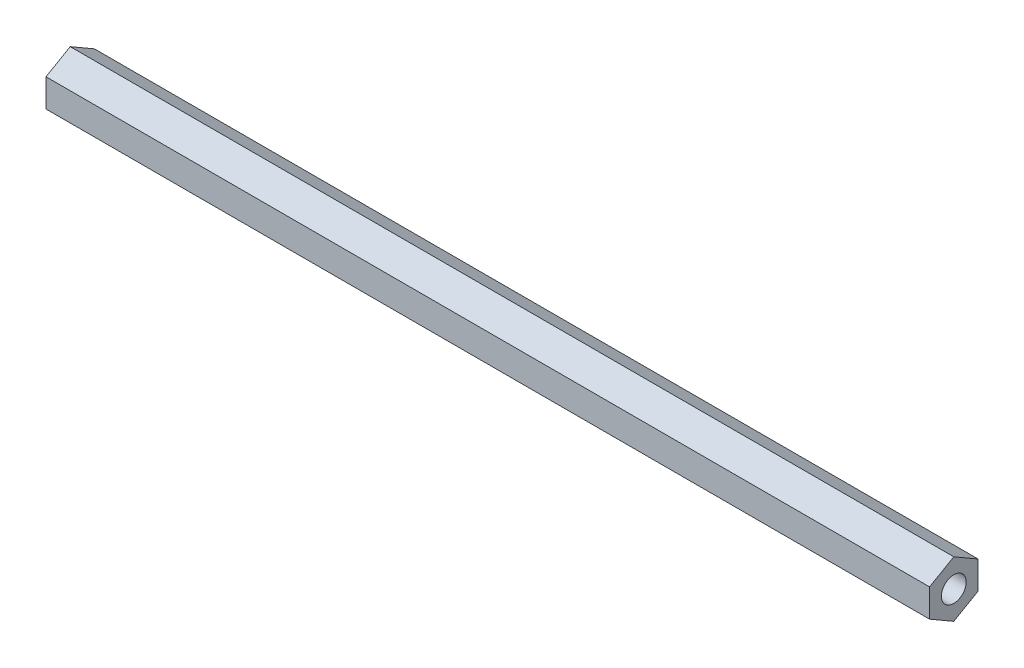
SolidWorks part; units mm, degrees
material "3003 Alloy"
ref_plane "Front Plane" through (0, 0, 0) normal (0, 0, 1) x (1, 0, 0)
ref_plane "Top Plane" through (0, 0, 0) normal (0, 1, 0) x (1, 0, 0)
ref_plane "Right Plane" through (0, 0, 0) normal (1, 0, 0) x (0, 0, -1)
sketch "Sketch1" plane through (0, 0, 0) normal (1, 0, 0) x (0, 0, -1)
  line L1 (0, 7.3323) -> (-6.35, 3.6662)
  line L2 (-6.35, 3.6662) -> (-6.35, -3.6662)
  line L3 (-6.35, -3.6662) -> (0, -7.3323)
  line L4 (0, -7.3323) -> (6.35, -3.6662)
  line L5 (6.35, -3.6662) -> (6.35, 3.6662)
  line L6 (6.35, 3.6662) -> (0, 7.3323)
  circle A0 centre (0, 0) radius 6.35 construction
  dimension "D1" = 12.7
extrude "Boss-Extrude1" add sketch "Sketch1" along normal blind 231.775
sketch "Sketch2" plane through (231.775, 0, 0) normal (1, 0, 0) x (0, 0, -1)
  circle A0 centre (0, 0) radius 3.2639
  dimension "D1" = 6.5278
extrude "Cut-Extrude1" cut sketch "Sketch2" against normal blind 12.7
sketch "Sketch3" plane through (0, 0, 0) normal (-1, 0, 0) x (0, 0, 1)
  circle A0 centre (0, 0) radius 3.2639
  dimension "D1" = 6.5278
extrude "Cut-Extrude2" cut sketch "Sketch3" against normal blind 12.7
